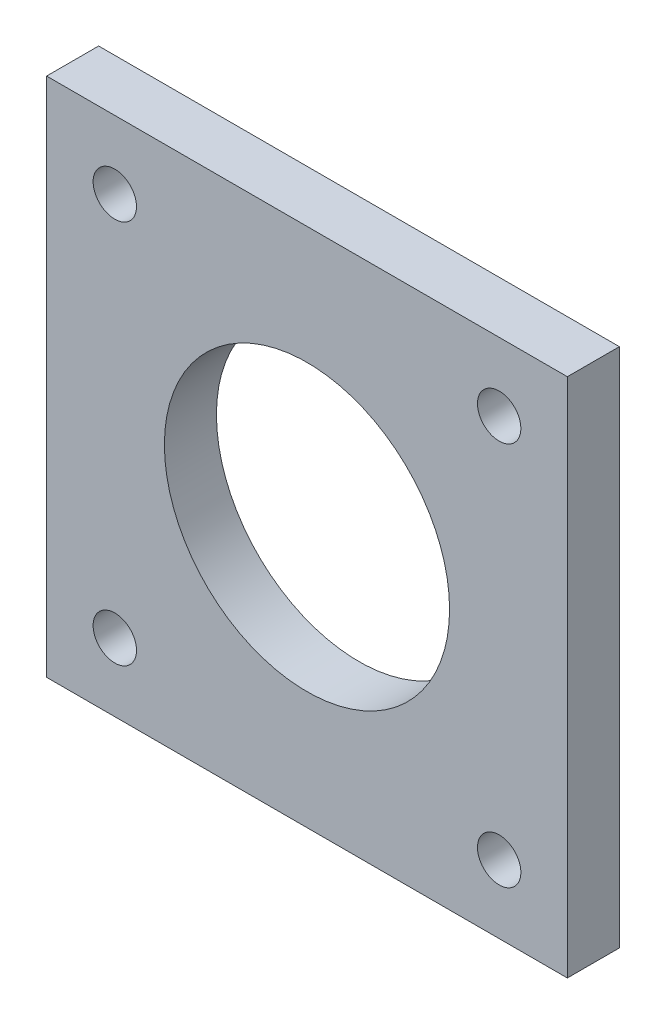
SolidWorks part; units mm, degrees
ref_plane "Front Plane" through (0, 0, 0) normal (0, 0, 1) x (1, 0, 0)
ref_plane "Top Plane" through (0, 0, 0) normal (0, 1, 0) x (1, 0, 0)
ref_plane "Right Plane" through (0, 0, 0) normal (1, 0, 0) x (0, 0, -1)
sketch "Sketch1" plane through (0, 0, 0) normal (0, 0, 1) x (1, 0, 0)
  line L1 (-21, -21) -> (21, -21)
  line L2 (-21, -21) -> (-21, 21)
  line L3 (-21, 21) -> (21, 21)
  line L4 (21, -21) -> (21, 21)
  line L5 (0, 21) -> (0, -21) construction
  line L6 (-21, 0) -> (21, 0) construction
  line L7 (-15.5, -15.5) -> (15.5, -15.5) construction
  line L8 (-15.5, -15.5) -> (-15.5, 15.5) construction
  line L9 (-15.5, 15.5) -> (15.5, 15.5) construction
  line L10 (15.5, -15.5) -> (15.5, 15.5) construction
  line L11 (-15.5, -15.5) -> (15.5, 15.5) construction
  line L12 (-15.5, 15.5) -> (15.5, -15.5) construction
  circle A0 centre (0, 0) radius 11.5
  circle A1 centre (-15.5, 15.5) radius 1.75
  circle A2 centre (15.5, 15.5) radius 1.75
  circle A3 centre (15.5, -15.5) radius 1.75
  circle A4 centre (-15.5, -15.5) radius 1.75
  point P0 (0, 0)
  point P4 (0, 0)
  dimension "D2" = 23
  dimension "D4" = 3.5
  dimension "D1" = 31
  dimension "D3" = 42
extrude "Boss-Extrude1" add sketch "Sketch1" along normal blind 4.1961 contours L1 L4 L3 L2 A0
